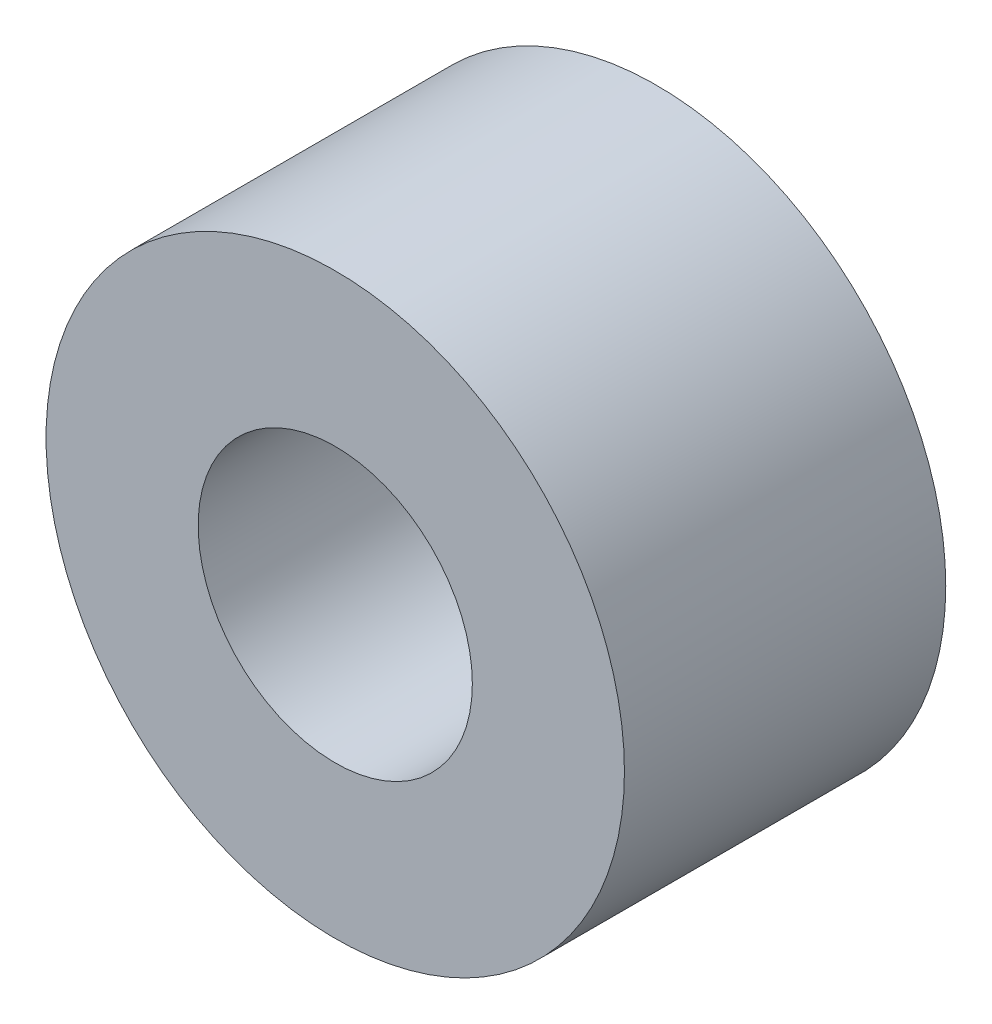
SolidWorks part; units mm, degrees
ref_plane "Front Plane" through (0, 0, 0) normal (0, 0, 1) x (1, 0, 0)
ref_plane "Top Plane" through (0, 0, 0) normal (0, 1, 0) x (1, 0, 0)
ref_plane "Right Plane" through (0, 0, 0) normal (1, 0, 0) x (0, 0, -1)
sketch "Sketch1" plane through (0, 0, 0) normal (0, 0, 1) x (1, 0, 0)
  circle A0 centre (0, 0) radius 2.1333
  circle A1 centre (0, 0) radius 4.5
  dimension "D1" = 9
extrude "Boss-Extrude1" add sketch "Sketch1" along normal blind 5
